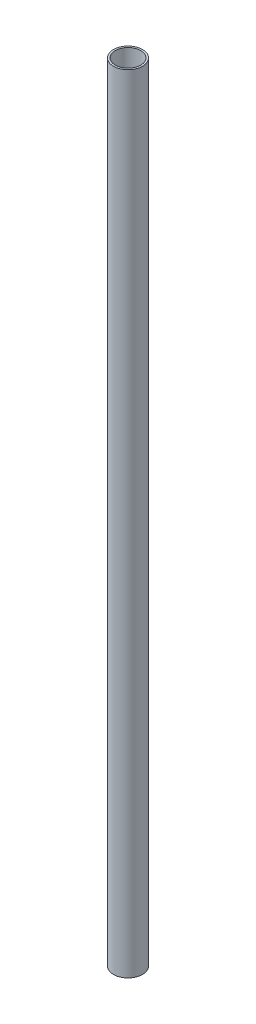
SolidWorks part; units mm, degrees
material "Plain Carbon Steel"
ref_plane "Front Plane" through (0, 0, 0) normal (0, 0, 1) x (1, 0, 0)
ref_plane "Top Plane" through (0, 0, 0) normal (0, 1, 0) x (1, 0, 0)
ref_plane "Right Plane" through (0, 0, 0) normal (1, 0, 0) x (0, 0, -1)
sketch "Sketch1" plane through (0, -521.3274, 0) normal (0, 1, 0) x (1, 0, 0)
  circle A2 centre (0, 0) radius 9.525
  circle A3 centre (0, 0) radius 8.325
  dimension "D1" = 19.05
  dimension "D2" = 1.2
extrude "Extrude1" add sketch "Sketch1" along normal blind 516
sketch3d "3DSketch1"
  line L0 (0, -521.3274, 0) -> (0, -53.3274, 0) construction
  line L1 (0, -5.3274, 0) -> (0, -521.3274, 0) construction
  line L2 (0, -5.3274, 0) -> (0, -521.3274, 0) construction
sketch "Sketch2" plane through (0, -5.3274, 0) normal (0, 1, 0) x (1, 0, 0)
  line B0 (-56.0122, 0) -> (55.8692, 0) construction
  spline B1 degree 3 poles (36.5981, 0) (36.5981, 7.0708) (11.784, 11.0469) (-22.9254, 11.1631) (-39.9421, 3.0559) (-51.6775, 0) knots 0 0 0 0 0.332614 0.432614 1 1 1 1
  spline B2 degree 3 poles (36.5981, 0) (36.5981, -7.0708) (11.784, -11.0469) (-22.9254, -11.1631) (-39.9421, -3.0559) (-51.6775, 0) knots 0 0 0 0 0.332614 0.432614 1 1 1 1
sketch_block_instance "SuspensionFairing-1"
sketch_block "SuspensionFairing"
extrude "Boss-Extrude1" [suppressed] add sketch "Sketch2" against normal up to surface (516 mm away) separate body
shell "Shell1" [suppressed] thickness 1.5
